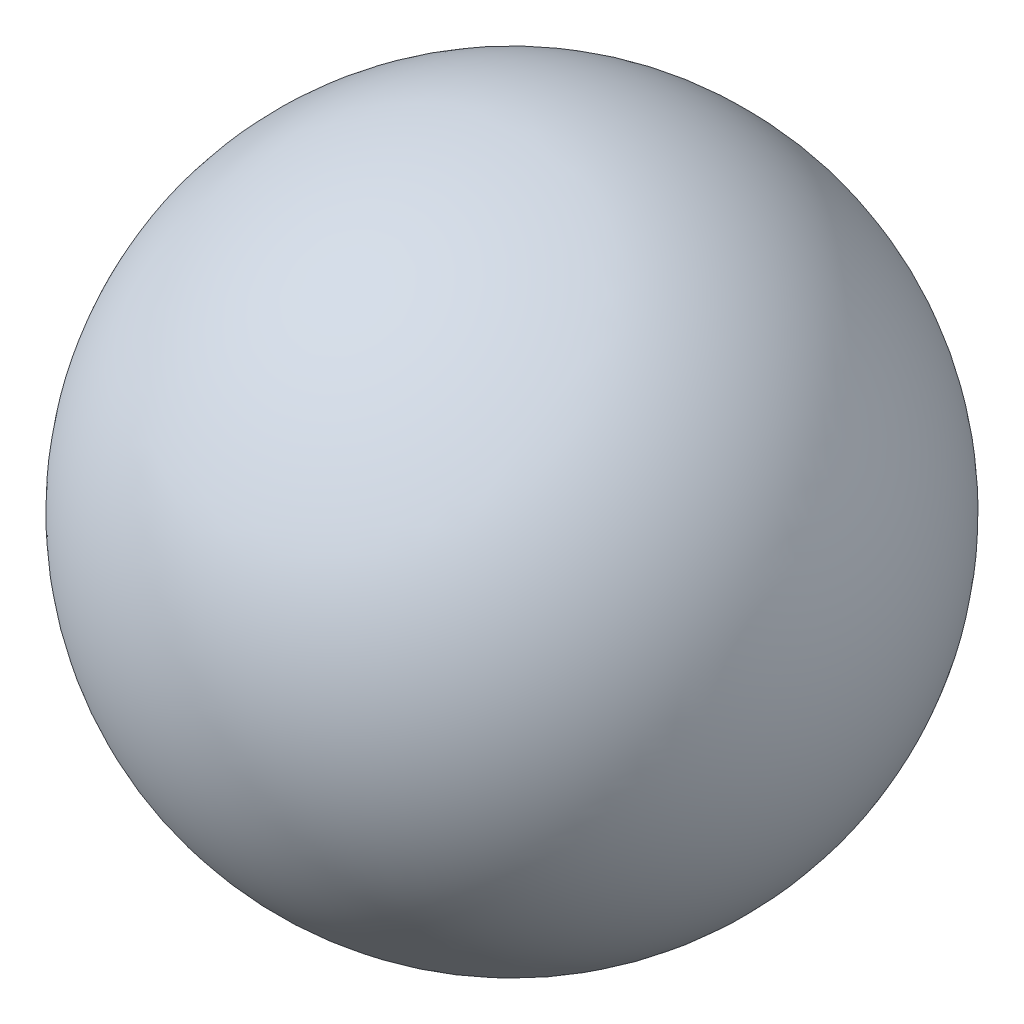
SolidWorks part; units mm, degrees
ref_plane "Front Plane" through (0, 0, 0) normal (0, 0, 1) x (1, 0, 0)
ref_plane "Top Plane" through (0, 0, 0) normal (0, 1, 0) x (1, 0, 0)
ref_plane "Right Plane" through (0, 0, 0) normal (1, 0, 0) x (0, 0, -1)
sketch "Sketch1" plane through (0, 0, 0) normal (0, 0, 1) x (1, 0, 0)
  line L0 (-6.1731, 0) -> (5.9251, 0) construction
  line L1 (-6, 0) -> (6, 0)
  arc A0 (6, 0) -> (-6, 0) centre (0, 0) ccw
  dimension "D1" = 12
revolve "Revolve3" add sketch "Sketch1" angle 360 about L0
